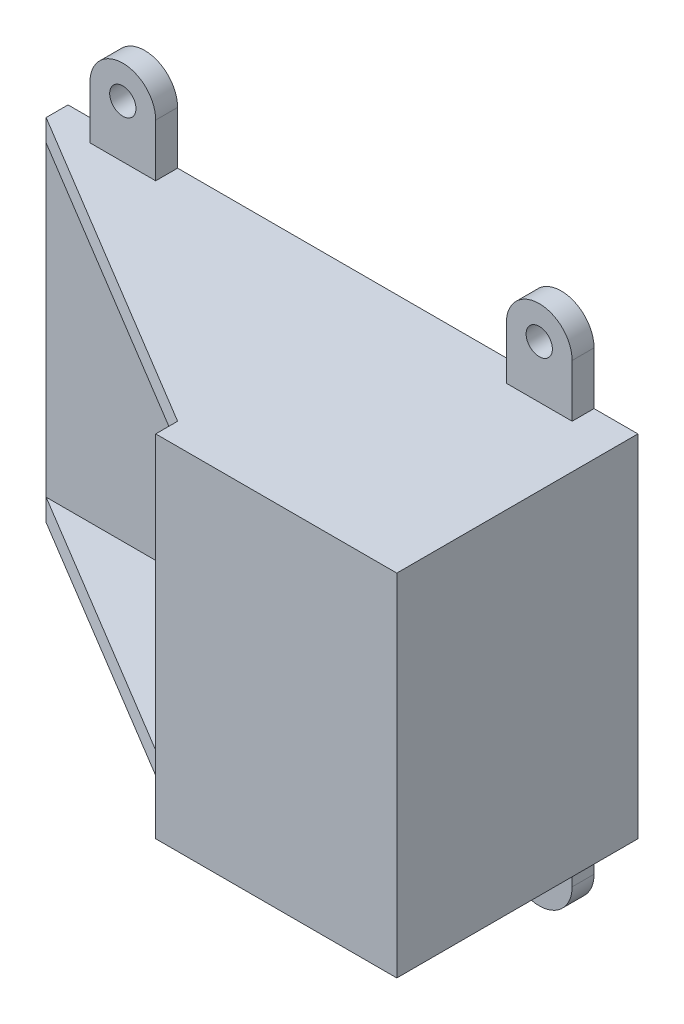
SolidWorks part; units mm, degrees
ref_plane "前基準面" through (0, 0, 0) normal (0, 0, 1) x (1, 0, 0)
ref_plane "上基準面" through (0, 0, 0) normal (0, 1, 0) x (1, 0, 0)
ref_plane "右基準面" through (0, 0, 0) normal (1, 0, 0) x (0, 0, -1)
sketch "草圖1" plane through (0, 0, 0) normal (0, 0, 1) x (1, 0, 0)
  line L0 (0, 35) -> (127.4955, 35) construction
  line L1 (0, 0) -> (125, 0)
  line L2 (0, 0) -> (0, 70)
  line L3 (0, 70) -> (125, 70)
  line L4 (125, 0) -> (125, 70)
  dimension "D1" = 70
  dimension "D2" = 125
extrude "填料-伸長1" add sketch "草圖1" along normal blind 5
sketch "草圖2" plane through (0, 0, 0) normal (0, -1, 0) x (1, 0, 0)
  line L0 (75, 50) -> (0, 5)
  line L1 (125, 0) -> (125, 50)
  line L2 (125, 50) -> (75, 50)
  line L4 (0, 5) -> (0, 0)
  line L5 (0, 0) -> (125, 0)
  dimension "D1" = 50
  dimension "D2" = 50
extrude "填料-伸長2" add sketch "草圖2" along normal blind 5
sketch "草圖3" plane through (0, 0, 5) normal (0, 0, 1) x (1, 0, 0)
  line L0 (0, 35) -> (125, 35)
  line L1 (0, 70) -> (0, 0) construction
  line L2 (125, 0) -> (125, 70) construction
  point P6 (0, 0)
pattern_linear "直線複製排列1" count 2 spacing 75 along (0, 1, 0) of "填料-伸長2"
sketch "草圖4" plane through (125, 0, 0) normal (1, 0, 0) x (0, 0, -1)
  line L1 (0, -5) -> (-50, -5)
  line L2 (0, -5) -> (0, 75)
  line L3 (0, 75) -> (-50, 75)
  line L4 (-50, -5) -> (-50, 75)
extrude "填料-伸長3" add sketch "草圖4" along normal blind 5
sketch "草圖5" plane through (0, 0, 50) normal (0, 0, 1) x (1, 0, 0)
  line L0 (130, 75) -> (75, 75) construction
  line L1 (130, -5) -> (75, -5)
  line L2 (130, -5) -> (130, 75)
  line L3 (130, 75) -> (75, 75)
  line L4 (75, -5) -> (75, 75)
  dimension "D1" = 55
extrude "填料-伸長4" add sketch "草圖5" along normal blind 5
sketch "草圖6" plane through (0, 0, 0) normal (0, 0, 1) x (1, 0, 0)
  line L0 (0, -5) -> (130, -5) construction
  line L1 (10, -5) -> (25, -5)
  line L2 (10, -5) -> (10, -17)
  line L3 (10, -17) -> (25, -17)
  line L4 (25, -5) -> (25, -17)
  circle A0 centre (17.5, -17) radius 7.5
  circle A1 centre (17.5, -17) radius 3
  dimension "D1" = 6
  dimension "D2" = 15
  dimension "D3" = 12
  dimension "D4" = 10
extrude "填料-伸長5" add sketch "草圖6" along normal blind 5 contours A0 L4 L1 L2 | A1 L3 A0 | A1 L3 A0
pattern_linear "直線複製排列2" count 2 spacing 95 along (1, 0, 0) of "填料-伸長5"
ref_plane "平面1" through (0, 35, 0) normal (0, 1, 0) x (1, 0, 0)
mirror "鏡射1" about plane through (0, 35, 0) normal (0, 1, 0) of "直線複製排列2", "填料-伸長5"
